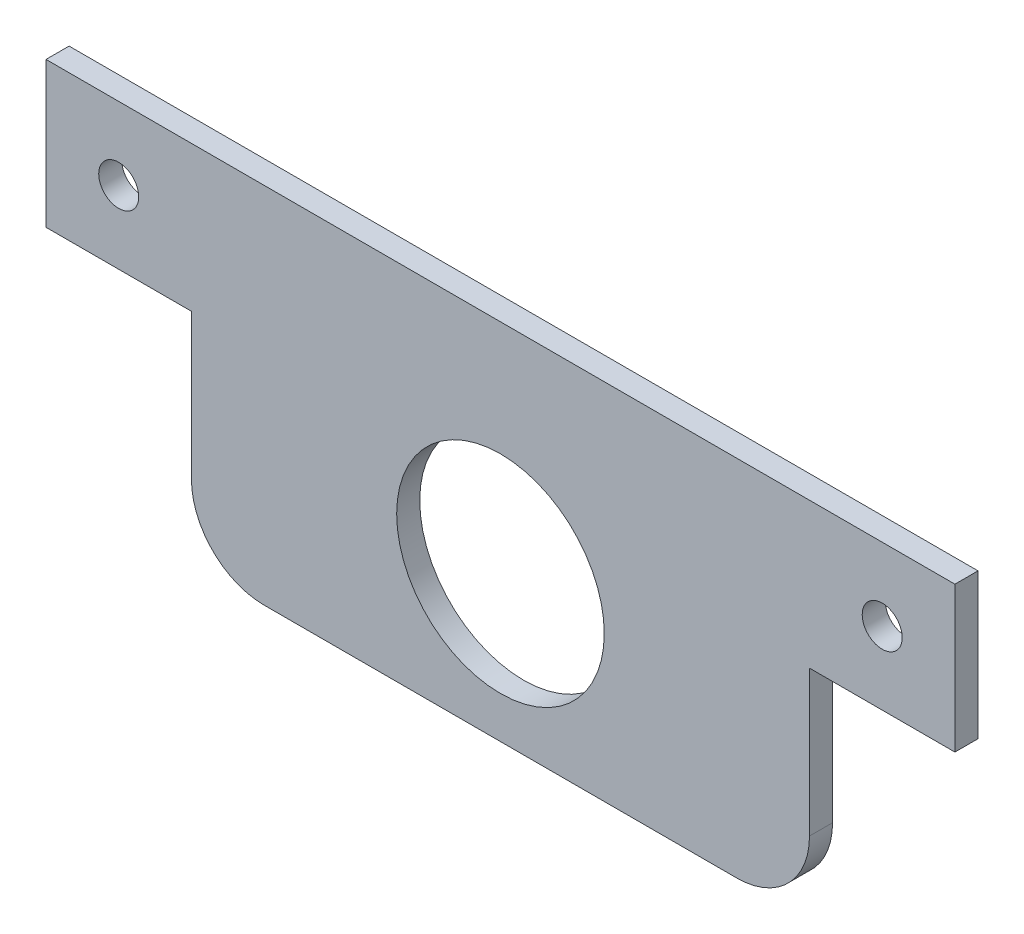
SolidWorks part; units mm, degrees
ref_plane "Front Plane" through (0, 0, 0) normal (0, 0, 1) x (1, 0, 0)
ref_plane "Top Plane" through (0, 0, 0) normal (0, 1, 0) x (1, 0, 0)
ref_plane "Right Plane" through (0, 0, 0) normal (1, 0, 0) x (0, 0, -1)
sketch "Sketch1" plane through (0, 0, 0) normal (0, 0, 1) x (1, 0, 0)
  line L1 (0, 0) -> (125, 0)
  line L2 (0, 0) -> (0, 50)
  line L3 (0, 50) -> (125, 50)
  line L4 (125, 0) -> (125, 50)
  dimension "D1" = 50
  dimension "D2" = 125
extrude "Boss-Extrude1" add sketch "Sketch1" along normal blind 3.175
sketch "Sketch2" plane through (0, 0, 3.175) normal (0, 0, 1) x (1, 0, 0)
  line L3 (0, 0) -> (125, 0) construction
  line L4 (62.5, 0) -> (62.5, 59.4224) construction
  line L5 (0, 0) -> (125, 0) construction
  circle A0 centre (62.5, 20) radius 14.275
  dimension "D1" = 28.55
  dimension "D2" = 20
extrude "Cut-Extrude1" cut sketch "Sketch2" against normal through all
sketch "Sketch6" plane through (0, 0, 0) normal (0, 0, -1) x (-1, 0, 0)
  line L0 (0, 50) -> (0, 0) construction
  line L1 (-125, 25) -> (0, 25) construction
  line L2 (-125, 0) -> (-125, 50) construction
  line L5 (-125, 0) -> (-105, 0)
  line L6 (-125, 0) -> (-125, 30)
  line L7 (-125, 30) -> (-105, 30)
  line L8 (-105, 0) -> (-105, 30)
  line L9 (0, 0) -> (-20, 0)
  line L10 (0, 0) -> (0, 30)
  line L11 (0, 30) -> (-20, 30)
  line L12 (-20, 0) -> (-20, 30)
  circle A0 centre (-115, 40) radius 2.75
  circle A1 centre (-10, 40) radius 2.75
  point P12 (-115, 30)
  dimension "D3" = 5.5
  dimension "D4" = 5.5
  dimension "D1" = 10
  dimension "D2" = 10
  dimension "D5" = 10
  dimension "D6" = 20
  dimension "D7" = 30
  dimension "D8" = 20
  dimension "D9" = 30
extrude "Cut-Extrude6" cut sketch "Sketch6" against normal through all
fillet "Fillet1" radius 10 2 edges at (20, 0, 1.5875) (105, 0, 1.5875)
